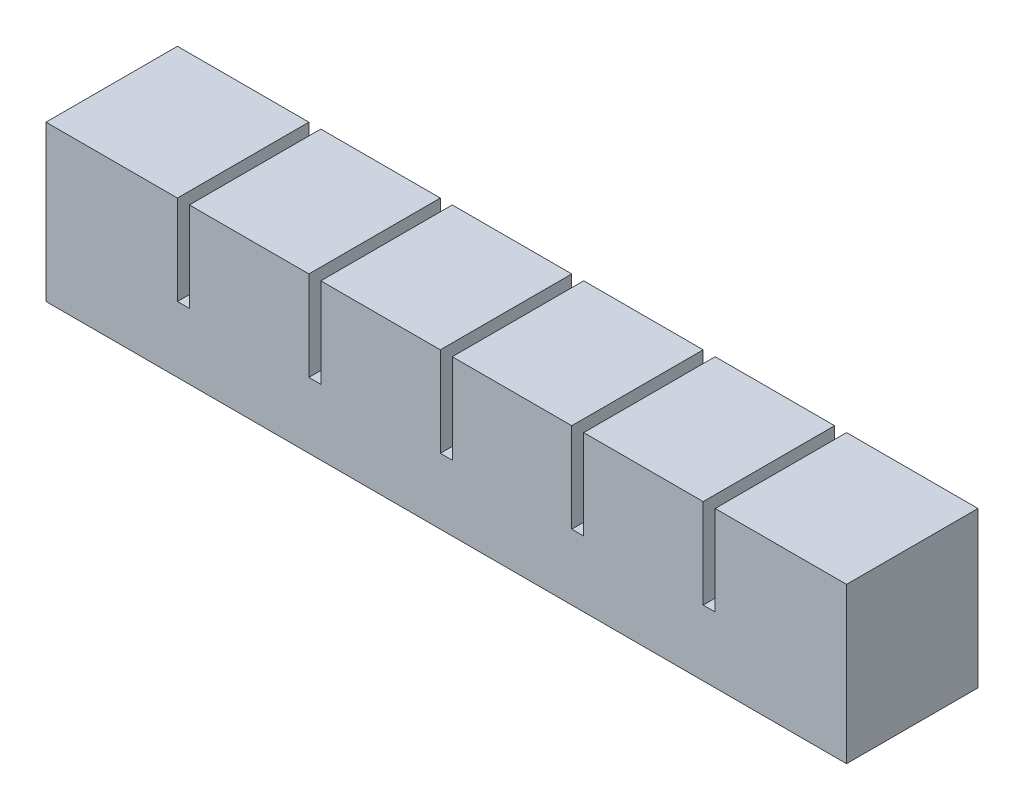
SolidWorks part; units mm, degrees
ref_plane "Front Plane" through (0, 0, 0) normal (0, 0, 1) x (1, 0, 0)
ref_plane "Top Plane" through (0, 0, 0) normal (0, 1, 0) x (1, 0, 0)
ref_plane "Right Plane" through (0, 0, 0) normal (1, 0, 0) x (0, 0, -1)
sketch "Sketch1" plane through (0, 0, 0) normal (0, 0, 1) x (1, 0, 0)
  line L1 (0, 0) -> (20, 0)
  line L2 (0, 0) -> (0, 20)
  line L3 (0, 20) -> (20, 20)
  line L4 (20, 0) -> (20, 20)
  dimension "D1" = 20
  dimension "D2" = 20
extrude "Boss-Extrude1" add sketch "Sketch1" along normal blind 22
sketch "Sketch2" plane through (0, 0, 0) normal (0, -1, 0) x (1, 0, 0)
  line L0 (20, 22) -> (20, 0) construction
  line L1 (6, 16) -> (14, 16)
  line L2 (6, 16) -> (6, 6)
  line L3 (6, 6) -> (14, 6)
  line L4 (14, 16) -> (14, 6)
  line L5 (0, 22) -> (20, 22) construction
  line L6 (0, 22) -> (0, 0) construction
  line L7 (0, 0) -> (20, 0) construction
  point P4 (14, 11)
  dimension "D1" = 6
  dimension "D2" = 6
  dimension "D3" = 6
  dimension "D4" = 6
extrude "Cut-Extrude1" cut sketch "Sketch2" against normal blind 14
sketch "Sketch3" plane through (20, 0, 0) normal (1, 0, 0) x (0, 0, -1)
  line L0 (0, 0) -> (0, 20) construction
  line L1 (-22, 0) -> (0, 0)
  line L2 (-22, 0) -> (-22, 5)
  line L3 (-22, 5) -> (0, 5)
  line L4 (0, 0) -> (0, 5)
  dimension "D1" = 5
extrude "Boss-Extrude2" add sketch "Sketch3" along normal blind 2
pattern_linear "LPattern1" count 6 spacing 22 along (1, 0, 0) of bodies 103
combine bodies "Combine1" operation type add bodies to combine 104 105 106 107 108 103
sketch "Sketch4" plane through (130, 0, 0) normal (1, 0, 0) x (0, 0, -1)
  line L1 (-22, 5) -> (0, 5)
  line L2 (-22, 5) -> (-22, 20)
  line L3 (-22, 20) -> (0, 20)
  line L4 (0, 5) -> (0, 20)
extrude "Boss-Extrude3" add sketch "Sketch4" along normal up to surface (2 mm away) up to face at (132, 2.5, 11)
sketch "Sketch5" plane through (0, 0, 0) normal (-1, 0, 0) x (0, 0, 1)
  line L1 (0, 20) -> (22, 20)
  line L2 (0, 20) -> (0, 0)
  line L3 (0, 0) -> (22, 0)
  line L4 (22, 20) -> (22, 0)
extrude "Boss-Extrude4" add sketch "Sketch5" along normal blind 2
ref_point "Point1"
sketch "Sketch6" plane through (0, 0, 0) normal (0, -1, 0) x (-1, 0, 0)
  line L0 (-124, -6) -> (-124, -16) construction
  line L1 (-6, -10) -> (-124, -10)
  line L2 (-6, -10) -> (-6, -12)
  line L3 (-6, -12) -> (-124, -12)
  line L4 (-124, -10) -> (-124, -12)
  line L5 (-6, -10) -> (-124, -12) construction
  line L6 (-6, -12) -> (-124, -10) construction
  point P0 (-65, -11)
  dimension "D1" = 2
extrude "Cut-Extrude2" cut sketch "Sketch6" against normal blind 2
sketch "Sketch7" plane through (0, 0, 0) normal (0, -1, 0) x (-1, 0, 0)
  line L1 (2, -22) -> (-132, -22)
  line L2 (2, -22) -> (2, 0)
  line L3 (2, 0) -> (-132, 0)
  line L4 (-132, -22) -> (-132, 0)
extrude "Boss-Extrude5" add sketch "Sketch7" along normal blind 6
